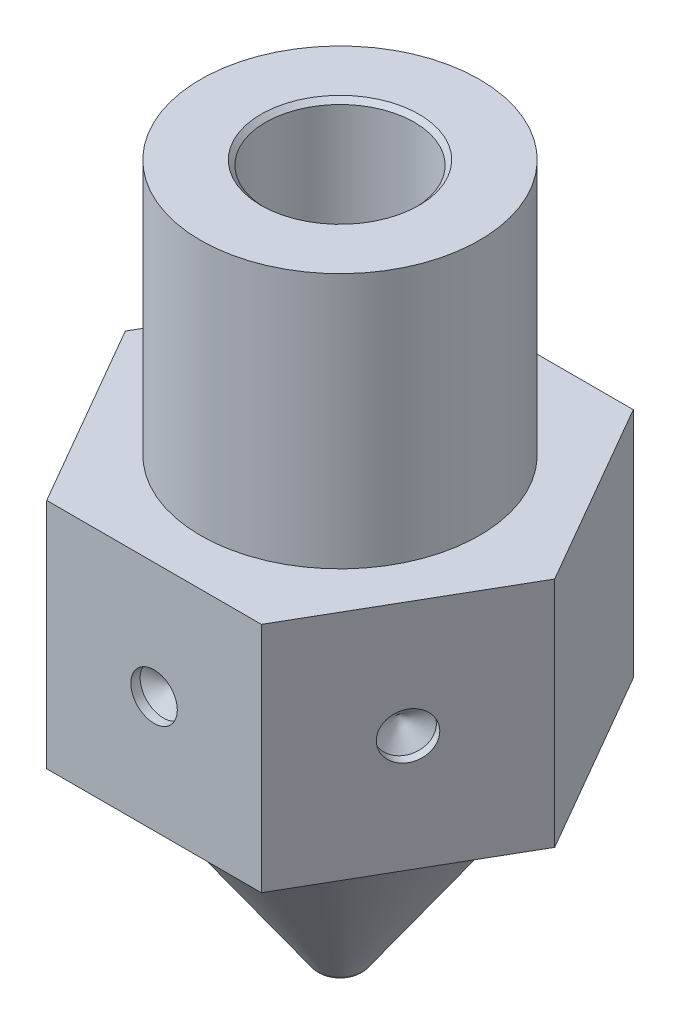
SolidWorks part; units mm, degrees
material "Latón"
ref_plane "Alzado" through (0, 0, 0) normal (0, 0, 1) x (1, 0, 0)
ref_plane "Planta" through (0, 0, 0) normal (0, 1, 0) x (1, 0, 0)
ref_plane "Vista lateral" through (0, 0, 0) normal (1, 0, 0) x (0, 0, -1)
sketch "Croquis1" plane through (0, 0, 0) normal (0, 0, 1) x (1, 0, 0)
  line L0 (0.2, 0) -> (0.25, 0)
  line L1 (0.4957, 0.1279) -> (3.5571, 4.5)
  line L2 (0.2, 0.8) -> (1.6, 2.7994)
  line L3 (7.0581, 9.5) -> (3, 9.5)
  line L4 (3, 9.5) -> (3, 15)
  line L5 (3, 15) -> (1.6, 15)
  line L6 (1.6, 15) -> (1.6, 2.7994)
  line L7 (0.2, 0.8) -> (0.2, 0)
  line L8 (0, 0) -> (0, 18.2336) construction
  line L11 (3.5571, 4.5) -> (5.706, 4.5)
  line L12 (5.706, 7.569) -> (5.706, 4.5)
  line L13 (5.706, 7.569) -> (7.0581, 9.5)
  arc A0 (0.25, 0) -> (0.4957, 0.1279) centre (0.25, 0.3) ccw
  point P14 (0.4062, 0)
  dimension "D8" = 0.05
  dimension "D10" = 0.3
  dimension "D1" = 0.2
  dimension "D3" = 1.6
  dimension "D4" = 3
  dimension "D5" = 15
  dimension "D6" = 5.5
  dimension "D7" = 35
  dimension "D9" = 0.8
  dimension "D13" = 4.5
revolve "Revolución1" add sketch "Croquis1" angle 360 about L8
cosmetic thread "Rosca cosmética1" parameters "D2"=4.891
sketch "Croquis2" plane through (0, 9.5, 0) normal (0, 1, 0) x (1, 0, 0)
  line L1 (2.3094, 4) -> (-2.3094, 4)
  line L2 (-2.3094, 4) -> (-4.6188, 0)
  line L3 (-4.6188, 0) -> (-2.3094, -4)
  line L4 (-2.3094, -4) -> (2.3094, -4)
  line L5 (2.3094, -4) -> (4.6188, 0)
  line L6 (4.6188, 0) -> (2.3094, 4)
  circle A0 centre (0, 0) radius 4 construction
  circle A2 centre (0, 0) radius 7.0581 construction
  circle A3 centre (0, 0) radius 7.0581
  dimension "D1" = 8
extrude "Cortar-Extruir1" cut sketch "Croquis2" against normal blind 7 from offset 1
chamfer "Chaflán1" distance 0.1 angle 45 1 edges at (0, 15, -1.6)
ref_plane "Plano1" through (4.6188, 4.5, 0) normal (0, 1, 0) x (1, 0, 0)
sketch "Croquis3" plane through (0, 0, 4) normal (0, 0, 1) x (1, 0, 0)
  line L0 (-2.3094, 9.5) -> (2.3094, 4.5) construction
  point P4 (0, 7)
sketch "Croquis4" plane through (3.4641, 0, 2) normal (0.866, 0, 0.5) x (0.5, 0, -0.866)
  line L0 (-2.3094, 9.5) -> (2.3094, 4.5) construction
  point P4 (0, 7)
hole_wizard "Diámetro de taladro Ø1.0 (1)1" positions "Croquis3D1" profile "Croquis5" hole size "Ø1.0" standard "Din"
sketch3d "Croquis3D1"
  point P0 (3.4641, 7, 2)
  point P3 (0, 7, 4)
sketch "Croquis5" plane through (3.4641, 7, 2) normal (0, 1, 0) x (0.5, 0, -0.866)
  line L0 (0, 0) -> (0, 0.5004)
  line L1 (0, 0.5004) -> (0.5, 0.2)
  line L2 (0.5, 0.2) -> (0.5, 0)
  line L5 (0.5, 0) -> (0, 0)
  line L10 (0, 0.5004) -> (-0.5, 0.2) construction
  line L11 (0, -6.35) -> (0, 107.95) construction
  dimension "Diámetro de taladro" = 1
  dimension "Profundidad de taladro" = 0.2
  dimension "Ángulo de perforador" = 118
sketch "Croquis6" plane through (0, 0, 0) normal (0, 0, 1) x (1, 0, 0)
  line L0 (2.4628, 14.65) -> (6.0569, 12.5749)
  line L1 (6.0569, 12.5749) -> (6.0569, 15)
  line L2 (2.4628, 14.65) -> (2.4628, 15)
  line L4 (6.0569, 9.5) -> (2.4628, 9.5)
  line L5 (2.4628, 9.5) -> (2.4628, 9.85)
  line L6 (2.4628, 9.85) -> (6.0569, 11.9251)
  line L7 (6.0569, 11.9251) -> (6.0569, 9.5)
  line L8 (2.3094, 9.5) -> (4.6188, 9.5) construction
  line L9 (0, 9.3842) -> (0, 14.2501) construction
  line L10 (2.4628, 15) -> (6.0569, 15)
  line L11 (3, 15) -> (-3, 15) construction
  dimension "D1" = 30
  dimension "D2" = 0.35
revolve "Cortar-Revolución1" [suppressed] cut sketch "Croquis6" angle 360 about L9
